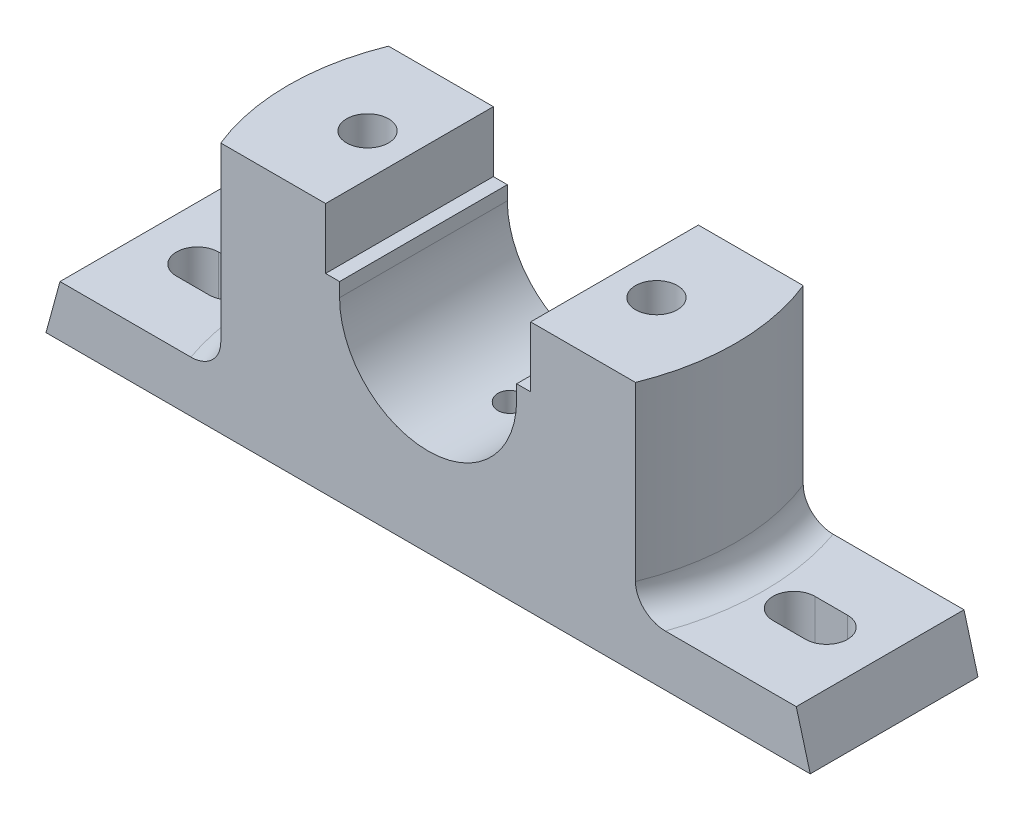
SolidWorks part; units mm, degrees
ref_plane "Front Plane" through (0, 0, 0) normal (0, 0, 1) x (1, 0, 0)
ref_plane "Top Plane" through (0, 0, 0) normal (0, 1, 0) x (1, 0, 0)
ref_plane "Right Plane" through (0, 0, 0) normal (1, 0, 0) x (0, 0, -1)
sketch "Sketch1" plane through (0, 0, 0) normal (0, 0, 1) x (1, 0, 0)
  line L0 (0, 0) -> (0, 65.8067) construction
  line L1 (-82, 0) -> (82, 0)
  line L2 (82, 0) -> (79, 11)
  line L3 (79, 11) -> (50, 11)
  line L4 (50, 11) -> (50, 54)
  line L5 (50, 54) -> (22, 54)
  line L6 (22, 54) -> (22, 41)
  line L7 (22, 41) -> (19, 41)
  line L8 (-22, 41) -> (-19, 41)
  line L9 (-22, 54) -> (-22, 41)
  line L10 (-50, 54) -> (-22, 54)
  line L11 (-50, 11) -> (-50, 54)
  line L12 (-79, 11) -> (-50, 11)
  line L13 (-82, 0) -> (-79, 11)
  line L14 (-19, 41) -> (-19, 38)
  line L15 (19, 41) -> (19, 38)
  arc A0 (-19, 38) -> (19, 38) centre (0, 38) ccw
  dimension "D8" = 13
  dimension "D1" = 164
  dimension "D2" = 11
  dimension "D3" = 3
  dimension "D4" = 54
  dimension "D5" = 44
  dimension "D6" = 38
  dimension "D7" = 50
  dimension "D9" = 16
extrude "Boss-Extrude1" add sketch "Sketch1" against normal mid plane 36
sketch "Sketch5" plane through (0, 54, 0) normal (0, 1, 0) x (1, 0, 0)
  line L0 (-44.3194, 18.4334) -> (-50, 18)
  line L3 (-50, 18) -> (-50, -18)
  line L4 (-50, -18) -> (-44.3194, -18.4334)
  arc A0 (-44.3194, 18.4334) -> (-44.3194, -18.4334) centre (0, 0) ccw
  dimension "D1" = 48
extrude "Cut-Extrude4" cut sketch "Sketch5" against normal up to surface (43 mm away) up to face at (-64.5, 11, 0)
sketch "Sketch6" plane through (0, 11, 0) normal (0, 1, 0) x (1, 0, 0)
  line L0 (-67.5, 0) -> (-60.5, 0) construction
  line L1 (-67.5, 4.5) -> (-60.5, 4.5)
  line L2 (-67.5, -4.5) -> (-60.5, -4.5)
  line L3 (0, -55) -> (0, 55) construction
  arc A0 (-67.5, 4.5) -> (-67.5, -4.5) centre (-67.5, 0) ccw
  arc A1 (-60.5, -4.5) -> (-60.5, 4.5) centre (-60.5, 0) ccw
  point P3 (-64, 0)
  dimension "D1" = 16
  dimension "D2" = 9
  dimension "D3" = 64
extrude "Cut-Extrude5" cut sketch "Sketch6" against normal through all
sketch "Sketch13" plane through (0, 0, 0) normal (0, -1, 0) x (1, 0, 0)
  line L1 (-41, -8.9603) -> (-21, -8.9603)
  line L2 (-41, -8.9603) -> (-41, 11.0397)
  line L3 (-41, 11.0397) -> (-21, 11.0397)
  line L4 (-21, -8.9603) -> (-21, 11.0397)
  line L5 (-41, -8.9603) -> (-21, 11.0397) construction
  line L6 (-41, 11.0397) -> (-21, -8.9603) construction
  point P0 (-31, 1.0397)
  dimension "D1" = 31
  dimension "D2" = 20
extrude "Cut-Extrude7" cut sketch "Sketch13" against normal blind 8
hole_wizard "Ø10.0mm Dowel Hole5" positions "Sketch19" profile "Sketch18" hole size "Ø10.0" standard "ANSI Metric"
sketch "Sketch19" plane through (0, 8, 0) normal (0, -1, 0) x (-1, 0, 0)
  point P0 (31, 0)
  dimension "D1" = 31
sketch "Sketch18" plane through (-31, 8, 0) normal (1, 0, 0) x (0, 0, -1)
  line L0 (0, 0) -> (0, 46)
  line L1 (0, 46) -> (4.5, 46)
  line L2 (4.5, 46) -> (4.5, 0)
  line L5 (4.5, 0) -> (0, 0)
  line L11 (0, -6.35) -> (0, 107.95) construction
  dimension "Thru Hole Dia." = 9
  dimension "Thru Hole Depth" = 46
mirror "Mirror3" about plane through (0, 0, 0) normal (1, 0, 0) of "Cut-Extrude5", "Ø10.0mm Dowel Hole5"
hole_wizard "Ø10.0mm Dowel Hole7" positions "3DSketch2" profile "Sketch24" hole size "Ø10.0" standard "ANSI Metric"
sketch3d "3DSketch2"
  point P1 (0, 19, 0)
  dimension "D1" = 0
  dimension "D2" = 0
sketch "Sketch24" plane through (0, 19, 0) normal (1, 0, 0) x (0, 0, 1)
  line L0 (0, 0) -> (0, 7.8026)
  line L1 (0, 7.8026) -> (3, 6)
  line L2 (3, 6) -> (3, 0)
  line L5 (3, 0) -> (0, 0)
  line L10 (0, 7.8026) -> (-3, 6) construction
  line L11 (0, -6.35) -> (0, 107.95) construction
  dimension "Hole Dia." = 6
  dimension "Hole Depth" = 6
  dimension "Drill Angle" = 118
sketch "Sketch25" plane through (0, 54, 0) normal (0, 1, 0) x (1, 0, 0)
  line L0 (44.4972, 18) -> (50, 18)
  line L1 (50, 18) -> (22, 18) construction
  line L2 (50, -18) -> (22, -18) construction
  line L3 (50, 18) -> (50, -18)
  line L4 (50, -18) -> (44.4972, -18)
  arc A0 (44.4972, -18) -> (44.4972, 18) centre (0, 0) ccw
  dimension "D1" = 48
extrude "Cut-Extrude8" cut sketch "Sketch25" against normal up to surface (43 mm away) up to face at (64.5, 11, 0)
fillet "Fillet2" radius 6 2 edges at (48, 11, 0) (-48, 11, 0)
mirror "Mirror4" about plane through (0, 0, 0) normal (1, 0, 0) of "Cut-Extrude7"
